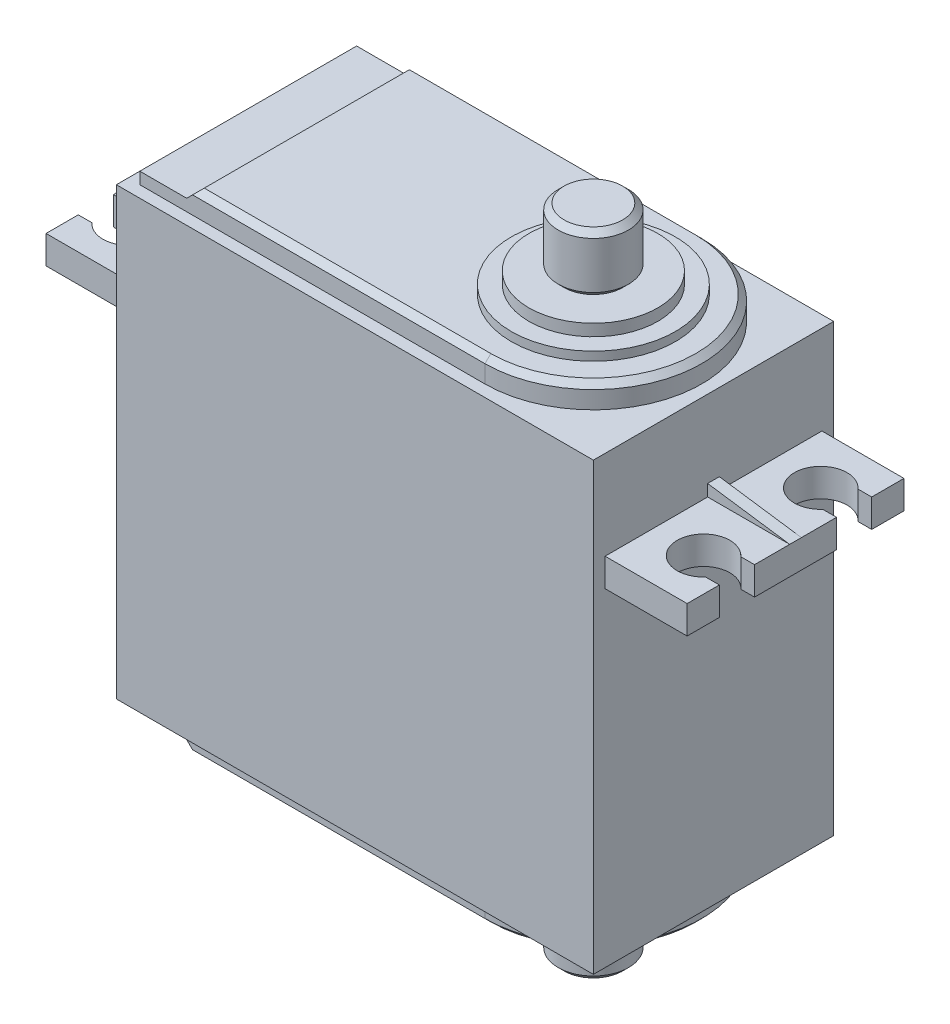
SolidWorks part; units mm, degrees
material "PE High Density"
ref_plane "Alzado" through (0, 0, 0) normal (0, 0, 1) x (1, 0, 0)
ref_plane "Planta" through (0, 0, 0) normal (0, 1, 0) x (1, 0, 0)
ref_plane "Vista lateral" through (0, 0, 0) normal (1, 0, 0) x (0, 0, -1)
sketch "Croquis1" plane through (0, 0, 0) normal (0, 0, 1) x (1, 0, 0)
  line L1 (-20.35, -19) -> (20.35, -19)
  line L2 (-20.35, -19) -> (-20.35, 19)
  line L3 (-20.35, 19) -> (20.35, 19)
  line L4 (20.35, -19) -> (20.35, 19)
  line L5 (-20.35, -19) -> (20.35, 19) construction
  line L6 (-20.35, 19) -> (20.35, -19) construction
  point P0 (0, 0)
  dimension "D1" = 40.7
  dimension "D2" = 38
extrude "Saliente-Extruir1" add sketch "Croquis1" along normal mid plane 20.5
ref_plane "Plano1" through (0, 0, 9.25) normal (0, 0, 1) x (1, 0, 0)
sketch "Croquis2" plane through (0, 0, 9.25) normal (0, 0, 1) x (1, 0, 0)
  line L1 (-20.35, 11.4) -> (-27.35, 11.4)
  line L2 (-20.35, 11.4) -> (-20.35, 9)
  line L3 (-20.35, 9) -> (-27.35, 9)
  line L4 (-27.35, 11.4) -> (-27.35, 9)
  line L5 (-20.35, -19) -> (20.35, -19) construction
  line L6 (0, 19) -> (0, -19) construction
  line L7 (20.35, 19) -> (-20.35, 19) construction
  line L8 (20.35, 11.4) -> (20.35, 9)
  line L9 (20.35, 9) -> (27.35, 9)
  line L10 (27.35, 11.4) -> (27.35, 9)
  line L11 (20.35, 11.4) -> (27.35, 11.4)
  line L12 (-20.35, 19) -> (-20.35, -19) construction
  dimension "D1" = 2.4
  dimension "D2" = 7
  dimension "D3" = 28
extrude "Saliente-Extruir2" add sketch "Croquis2" against normal blind 18.5
sketch "Croquis3" plane through (0, 0, 0) normal (0, 0, 1) x (1, 0, 0)
  line L0 (-20.35, 12.4) -> (-20.35, 11.4)
  line L2 (-20.35, 11.4) -> (-27.35, 11.4)
  line L3 (-27.35, 11.4) -> (-20.35, 12.4)
  line L4 (20.35, 12.4) -> (27.35, 11.4)
  line L6 (27.35, 11.4) -> (20.35, 11.4)
  line L7 (20.35, 11.4) -> (20.35, 12.4)
  line L8 (-20.35, 19) -> (-20.35, -19) construction
  line L9 (20.35, -19) -> (20.35, 19) construction
  dimension "D1" = 1
extrude "Saliente-Extruir3" add sketch "Croquis3" along normal mid plane 1
sketch "Croquis4" plane through (0, 11.4, 0) normal (0, 1, 0) x (1, 0, 0)
  line L0 (-27.35, 6.5) -> (-26.1771, 6.5)
  line L1 (-24.5, -5) -> (24.5, -5) construction
  line L2 (-24.5, -5) -> (-24.5, 5) construction
  line L3 (-24.5, 5) -> (24.5, 5) construction
  line L4 (24.5, -5) -> (24.5, 5) construction
  line L5 (-24.5, -5) -> (24.5, 5) construction
  line L6 (-24.5, 5) -> (24.5, -5) construction
  line L7 (-27.35, 9.25) -> (-27.35, 0.5) construction
  line L8 (-27.35, 3.5) -> (-26.1771, 3.5)
  line L9 (-27.35, -3.5) -> (-26.1771, -3.5)
  line L10 (-27.35, -0.5) -> (-27.35, -9.25) construction
  line L11 (-27.35, -6.5) -> (-26.1771, -6.5)
  line L12 (26.1771, -6.5) -> (27.35, -6.5)
  line L13 (27.35, -0.5) -> (27.35, -9.25) construction
  line L14 (27.35, -3.5) -> (26.1771, -3.5)
  line L15 (27.35, 3.5) -> (26.1771, 3.5)
  line L16 (27.35, 9.25) -> (27.35, 0.5) construction
  line L17 (27.35, 6.5) -> (26.1771, 6.5)
  line L18 (27.35, 6.5) -> (27.35, 3.5)
  line L19 (27.35, -3.5) -> (27.35, -6.5)
  line L20 (-27.35, -3.5) -> (-27.35, -6.5)
  line L21 (-27.35, 3.5) -> (-27.35, 6.5)
  line L22 (-27.35, 5) -> (-24.5, 5) construction
  line L23 (-24.5, -5) -> (-27.35, -5) construction
  line L24 (24.5, -5) -> (27.35, -5) construction
  line L25 (24.5, 5) -> (27.35, 5) construction
  arc A0 (26.1771, 6.5) -> (26.1771, 3.5) centre (24.5, 5) ccw
  arc A1 (26.1771, -3.5) -> (26.1771, -6.5) centre (24.5, -5) ccw
  arc A2 (-26.1771, -6.5) -> (-26.1771, -3.5) centre (-24.5, -5) ccw
  arc A3 (-26.1771, 3.5) -> (-26.1771, 6.5) centre (-24.5, 5) ccw
  point P0 (0, 0)
  dimension "D3" = 4.5
  dimension "D1" = 49
  dimension "D2" = 10
  dimension "D4" = 3
extrude "Cortar-Extruir1" cut sketch "Croquis4" against normal up to vertex (2.4 mm away)
sketch "Croquis6" plane through (0, 19, 0) normal (0, 1, 0) x (1, 0, 0)
  line L1 (20.35, 10.25) -> (-20.35, 10.25) construction
  line L2 (-20.35, -10.25) -> (-20.35, 10.25) construction
  line L3 (20.35, -10.25) -> (-20.35, -10.25) construction
  line L4 (20.35, -10.25) -> (20.35, 10.25) construction
  line L5 (20.35, 10.25) -> (-20.35, 10.25) construction
  line L6 (-20.35, -10.25) -> (-20.35, 10.25) construction
  line L7 (20.35, -10.25) -> (-20.35, -10.25) construction
  line L8 (20.35, -10.25) -> (20.35, 10.25) construction
  line L9 (10.1, 9.25) -> (-19.35, 9.25)
  line L10 (-19.35, -9.25) -> (-19.35, 9.25)
  line L11 (10.1, -9.25) -> (-19.35, -9.25)
  line L12 (19.35, -9.25) -> (19.35, 9.25) construction
  line L13 (19.35, 9.25) -> (-19.35, 9.25) construction
  line L14 (19.35, -9.25) -> (-19.35, -9.25) construction
  arc A0 (10.1, -9.25) -> (10.1, 9.25) centre (10.1, 0) ccw
  dimension "D1" = 1
extrude "Saliente-Extruir4" add sketch "Croquis6" along normal blind 2
sketch "Croquis9" plane through (0, 0, 9.25) normal (0, 0, 1) x (1, 0, 0)
  line L0 (-19.35, 21) -> (-19.35, 20)
  line L2 (-19.35, 20) -> (-15.35, 20)
  line L3 (-15.35, 20) -> (-14.35, 21)
  line L5 (-14.35, 21) -> (-19.35, 21)
  line L7 (-19.35, 21) -> (-19.35, 19) construction
  line L8 (-19.35, 21) -> (10.1, 21) construction
  dimension "D1" = 5
  dimension "D2" = 45
extrude "Cortar-Extruir3" cut sketch "Croquis9" against normal up to vertex
sketch "Croquis10" plane through (0, 21, 0) normal (0, 1, 0) x (1, 0, 0)
  circle A1 centre (10.1, 0) radius 7
  arc A2 (10.1, -9.25) -> (10.1, 9.25) centre (10.1, 0) ccw construction
  dimension "D1" = 14
extrude "Saliente-Extruir5" add sketch "Croquis10" along normal blind 0.75
sketch "Croquis11" plane through (0, 21.75, 0) normal (0, 1, 0) x (1, 0, 0)
  circle A0 centre (10.1, 0) radius 5.5
  circle A1 centre (10.1, 0) radius 7
  circle A2 centre (10.1, 0) radius 7 construction
  dimension "D1" = 0
  dimension "D2" = 1.5
extrude "Saliente-Extruir6" add sketch "Croquis11" along normal blind 1
sketch "Croquis12" plane through (0, 22.75, 0) normal (0, 1, 0) x (1, 0, 0)
  circle A0 centre (10.1, 0) radius 3
  circle A1 centre (10.1, 0) radius 5.5 construction
  dimension "D1" = 6
extrude "Saliente-Extruir7" add sketch "Croquis12" along normal blind 5
chamfer "Chaflán2" distance 0.5 angle 45 1 edges at (10.1, 27.75, 3)
sketch "Croquis13" plane through (0, 0, 0) normal (0, 0, 1) x (1, 0, 0)
  line L0 (7.1, 23.25) -> (7.1, 22.75)
  line L1 (7.1, 27.25) -> (7.1, 22.75) construction
  line L2 (7.1, 22.75) -> (7.6, 22.75)
  line L3 (15.6, 22.75) -> (4.6, 22.75) construction
  line L4 (7.6, 22.75) -> (7.1, 23.25)
  line L5 (7.6, 27.75) -> (7.1, 27.25) construction
  line L6 (10.1, 27.75) -> (10.1, 22.75) construction
  line L7 (12.6, 27.75) -> (7.6, 27.75) construction
revolve "Cortar-Revolución1" cut sketch "Croquis13" angle 360 about L6
mirror "Mirror1" about plane through (0, 0, 0) normal (0, 1, 0) of "Chaflán2", "Saliente-Extruir7", "Saliente-Extruir6", "Cortar-Extruir3", "Saliente-Extruir5", "Saliente-Extruir4"
